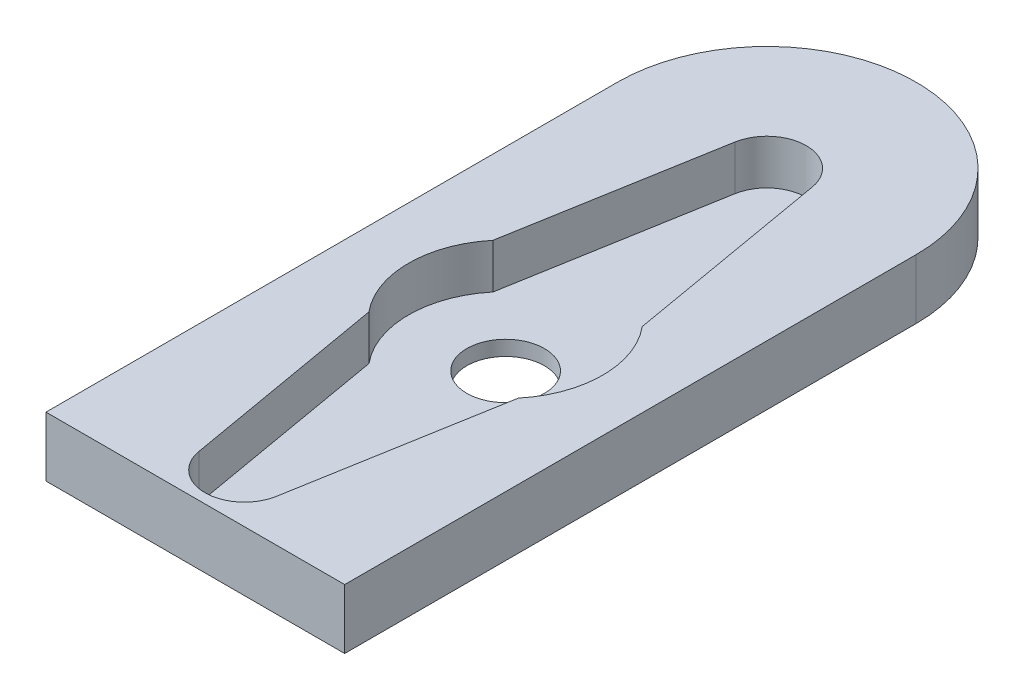
SolidWorks part; units mm, degrees
ref_plane "前基準面" through (0, 0, 0) normal (0, 0, 1) x (1, 0, 0)
ref_plane "上基準面" through (0, 0, 0) normal (0, 1, 0) x (1, 0, 0)
ref_plane "右基準面" through (0, 0, 0) normal (1, 0, 0) x (0, 0, -1)
sketch "草圖1" plane through (0, 0, 0) normal (0, 1, 0) x (1, 0, 0)
  line L0 (0, 0) -> (0, 38.27)
  line L1 (20, 38.27) -> (20, 0)
  line L2 (20, 0) -> (0, 0)
  arc A0 (0, 38.27) -> (20, 38.27) centre (10, 38.27) cw
  dimension "D1" = 38.27
  dimension "D2" = 20
sketch "草圖2" plane through (0, 0, 0) normal (0, 1, 0) x (1, 0, 0)
  line L0 (10, 18.502) -> (10, 26.9451) construction
  line L1 (0, 0) -> (0, 38.27) construction
  line L2 (20, 38.27) -> (20, 0) construction
  line L3 (7.4, 38.7224) -> (5, 24.9297)
  line L4 (12.6, 38.7224) -> (15, 24.9297)
  line L5 (4.9977, 16.6258) -> (7.4, 2.8335)
  line L6 (15.0023, 16.6258) -> (12.6, 2.8335)
  line L7 (10, 41.5789) -> (10, 0.5872) construction
  line L8 (10, 20.7763) -> (35.2864, 20.7763) construction
  arc A0 (12.6, 38.7224) -> (7.4, 38.7224) centre (10, 38.27) ccw
  arc A1 (5, 24.9297) -> (4.9977, 16.6258) centre (10, 20.7763) ccw
  arc A2 (7.4, 2.8335) -> (12.6, 2.8335) centre (10, 3.2863) ccw
  arc A3 (15.0023, 16.6258) -> (15, 24.9297) centre (10, 20.7763) ccw
  dimension "D1" = 14
  dimension "D2" = 20.1327
  dimension "D3" = 5
  dimension "D4" = 2.6
  dimension "D5" = 2.6
  dimension "D6" = 13
  dimension "D8" = 17.49
  dimension "D9" = 17.4937
sketch "草圖3" plane through (0, 0, 0) normal (0, 1, 0) x (1, 0, 0)
  circle A0 centre (10, 20.7763) radius 2.6
  dimension "D1" = 5.2
extrude "填料-伸長6" add sketch "草圖1" against normal blind 4 contours L0 A0 L1 L2
extrude "除料-伸長12" cut sketch "草圖2" against normal blind 3 contours L4 A3 L6 A2 L5 A1 L3 A0
extrude "除料-伸長13" cut sketch "草圖3" against normal blind 4 contours A0
sketch "草圖15" plane through (0, 0, 0) normal (0, 0, 1) x (1, 0, 0)
  arc A2 (0, 0) -> (20, 0) centre (10, -10) cw
  arc A3 (20, 0) -> (20, -4) centre (18, -2) cw
  arc A4 (20, -4) -> (0, -4) centre (10, 6) cw
  arc A5 (0, 0) -> (0, -4) centre (2, -2) ccw
ref_plane "平面2" through (0, 0, 30) normal (0, 0, 1) x (1, 0, 0)
ref_plane "平面3" through (0, -2, 0) normal (0, 1, 0) x (1, 0, 0)
ref_plane "平面5" through (10, 0, 0) normal (1, 0, 0) x (0, 0, -1)
ref_plane "平面17" through (0, 0, 80) normal (0, 0, 1) x (1, 0, 0)
sketch "草圖40" plane through (0, 0, 80) normal (0, 0, 1) x (1, 0, 0)
  line L0 (10, 4.7505) -> (10, -8.6988) construction
  line L2 (0, -4) -> (0, 0) construction
  line L3 (20, -4) -> (20, 0) construction
  point P6 (10.1552, -2.1121)
  dimension "D1" = 10
  dimension "D2" = 10
sketch "草圖41" plane through (0, 0, 80) normal (0, 0, 1) x (1, 0, 0)
  line L0 (10, 4.7505) -> (10, -8.6988) construction
  circle A0 centre (10, -1.9741) radius 0.25
  dimension "D1" = 0.5
sketch "草圖43" plane through (0, -2, 0) normal (0, 1, 0) x (1, 0, 0)
  line L0 (-0.8284, 0) -> (9.7513, -80)
  line L1 (20.8284, 0) -> (10.2487, -80)
  point P8 (0, 0)
sketch "草圖46" plane through (10, 0, 0) normal (1, 0, 0) x (0, 0, -1)
  line L0 (-80, 4.7505) -> (-80, -8.6988) construction
  arc A0 (0, 4.1421) -> (-80, -1.7241) centre (-38.5085, -19.1315) ccw
  arc A1 (0, -8.1421) -> (-80, -2.2241) centre (-38.4949, 15.1633) cw
  point P16 (-38.285, -28.359)
  dimension "D1" = 45
sketch "草圖47" plane through (0, 0, 0) normal (0, 0, 1) x (1, 0, 0)
  line L0 (-0.8284, -2) -> (20, -2) construction
  line L1 (20, -4) -> (20, 0) construction
other "邊界-曲面15"
